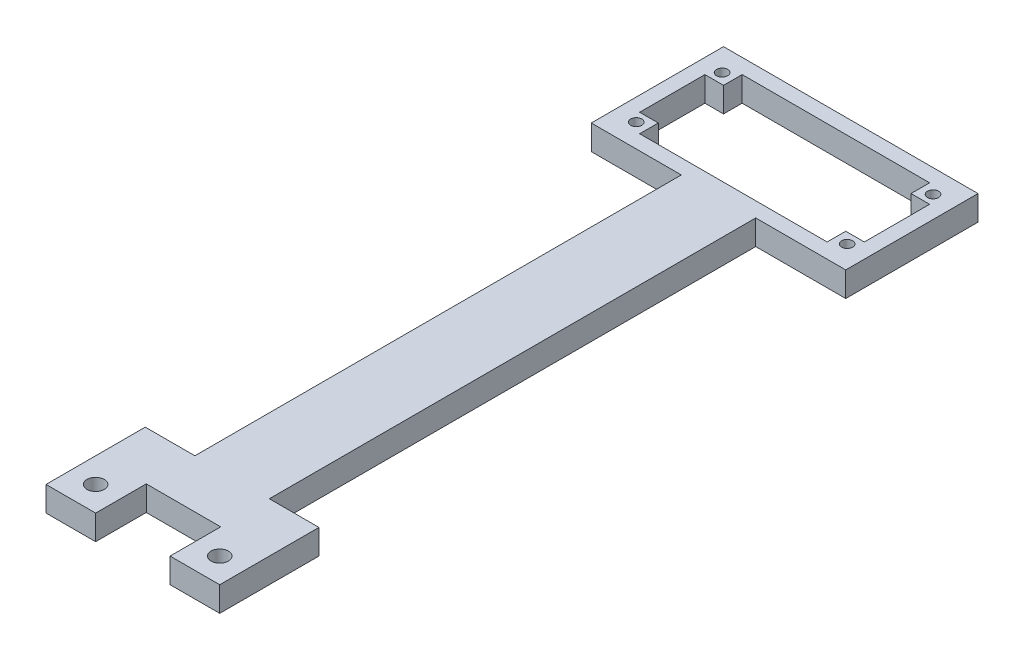
SolidWorks part; units mm, degrees
ref_plane "Front Plane" through (0, 0, 0) normal (0, 0, 1) x (1, 0, 0)
ref_plane "Top Plane" through (0, 0, 0) normal (0, 1, 0) x (1, 0, 0)
ref_plane "Right Plane" through (0, 0, 0) normal (1, 0, 0) x (0, 0, -1)
sketch "Sonic Sensor Reference Sketch" plane through (0, 0, 0) normal (0, 1, 0) x (1, 0, 0)
  line L1 (0, 0) -> (45.27, 0) construction
  line L2 (0, 0) -> (0, 20.65) construction
  line L3 (0, 20.65) -> (45.27, 20.65) construction
  line L4 (45.27, 0) -> (45.27, 20.65) construction
  dimension "D1" = 45.27
  dimension "D2" = 20.65
sketch "Sketch2" plane through (0, 0, 0) normal (0, 1, 0) x (1, 0, 0)
  line L8 (48.27, -3) -> (48.27, 23.65)
  line L9 (-3, -3) -> (48.27, -3)
  line L10 (-3, 23.65) -> (-3, -3)
  line L11 (48.27, 23.65) -> (-3, 23.65)
  line L12 (48.27, -3) -> (48.27, 23.65)
  line L13 (-3, -3) -> (48.27, -3)
  line L14 (-3, 23.65) -> (-3, -3)
  line L15 (48.27, 23.65) -> (-3, 23.65)
  dimension "D1" = 3
extrude "Boss-Extrude2" add sketch "Sketch2" along normal blind 5
sketch "Sketch3" plane through (0, 5, 0) normal (0, 1, 0) x (1, 0, 0)
  line L0 (0, 0) -> (45.27, 0) construction
  line L1 (45.27, 0) -> (45.27, 20.65) construction
  line L2 (0, 20.65) -> (45.27, 20.65) construction
  line L3 (0, 0) -> (0, 20.65) construction
  line L4 (0, 0) -> (45.27, 0)
  line L5 (45.27, 0) -> (45.27, 20.65)
  line L6 (0, 20.65) -> (45.27, 20.65)
  line L7 (0, 0) -> (0, 20.65)
extrude "Cut-Extrude1" cut sketch "Sketch3" against normal through all
sketch "Sketch4" plane through (0, 5, 0) normal (0, 1, 0) x (1, 0, 0)
  line L0 (1.385, 18.975) -> (43.885, 18.975) construction
  line L1 (22.635, 23.65) -> (22.635, -3) construction
  line L2 (48.27, 23.65) -> (-3, 23.65) construction
  line L3 (-3, -3) -> (48.27, -3) construction
  line L4 (-3, 10.325) -> (48.27, 10.325) construction
  line L5 (-3, 23.65) -> (-3, -3) construction
  line L6 (48.27, -3) -> (48.27, 23.65) construction
  line L7 (1.385, 18.975) -> (1.385, 1.675) construction
  line L8 (1.385, 1.675) -> (43.885, 1.675) construction
  line L9 (43.885, 1.675) -> (43.885, 18.975) construction
  line L11 (0, 20.65) -> (3.75, 20.65)
  line L12 (0, 20.65) -> (0, 16.9)
  line L13 (0, 16.9) -> (3.75, 16.9)
  line L14 (3.75, 20.65) -> (3.75, 16.9)
  line L15 (0, 0) -> (3.75, 0)
  line L16 (0, 0) -> (0, 3.75)
  line L17 (0, 3.75) -> (3.75, 3.75)
  line L18 (3.75, 0) -> (3.75, 3.75)
  line L19 (45.27, 0) -> (41.52, 0)
  line L20 (45.27, 0) -> (45.27, 3.75)
  line L21 (45.27, 3.75) -> (41.52, 3.75)
  line L22 (41.52, 0) -> (41.52, 3.75)
  line L23 (45.27, 20.65) -> (41.52, 20.65)
  line L24 (45.27, 20.65) -> (45.27, 16.9)
  line L25 (45.27, 16.9) -> (41.52, 16.9)
  line L26 (41.52, 20.65) -> (41.52, 16.9)
  circle A0 centre (1.385, 18.975) radius 1.12 construction
  circle A1 centre (43.885, 18.975) radius 1.12 construction
  circle A2 centre (1.385, 1.675) radius 1.12 construction
  circle A3 centre (43.885, 1.675) radius 1.12 construction
  point P17 (22.635, 18.975)
  point P18 (1.385, 10.325)
  point P42 (3.0106, 17.4014)
  dimension "D3" = 2.24
  dimension "D1" = 42.5
  dimension "D2" = 17.3
  dimension "D4" = 3.75
  dimension "D5" = 3.75
extrude "Boss-Extrude3" add sketch "Sketch4" against normal up to surface (5 mm away) up to face at (22.635, 0, -10.325)
sketch "Sketch5" plane through (0, 5, 0) normal (0, 1, 0) x (1, 0, 0)
  circle A0 centre (1.385, 18.975) radius 1.12
  circle A1 centre (43.885, 18.975) radius 1.12
  circle A2 centre (43.885, 1.675) radius 1.12
  circle A3 centre (1.385, 1.675) radius 1.12
  circle A4 centre (1.385, 18.975) radius 1.12 construction
  circle A5 centre (43.885, 18.975) radius 1.12 construction
  circle A6 centre (1.385, 1.675) radius 1.12 construction
  circle A7 centre (43.885, 1.675) radius 1.12 construction
extrude "Cut-Extrude2" cut sketch "Sketch5" against normal through all
sketch "Sketch6" plane through (0, 5, 0) normal (0, 1, 0) x (1, 0, 0)
  line L0 (-3, -3) -> (48.27, -3) construction
  line L1 (30.135, -3) -> (15.135, -3)
  line L2 (30.135, -3) -> (30.135, -111)
  line L3 (30.135, -111) -> (15.135, -111)
  line L4 (15.135, -3) -> (15.135, -111)
  point P6 (22.635, -3)
  point P7 (22.635, -3)
  point P8 (12.4878, -37.8436)
  dimension "D1" = 15
  dimension "D2" = 108
extrude "Boss-Extrude4" add sketch "Sketch6" against normal up to surface (5 mm away) up to face at (1.385, 0, -0.555)
sketch "Sketch7" plane through (0, 5, 0) normal (0, 1, 0) x (1, 0, 0)
  line L0 (30.135, -111) -> (30.135, -3) construction
  line L1 (30.135, -101) -> (40.135, -101)
  line L2 (30.135, -101) -> (30.135, -121)
  line L3 (30.135, -121) -> (40.135, -121)
  line L4 (40.135, -101) -> (40.135, -121)
  line L5 (15.135, -3) -> (15.135, -111) construction
  line L6 (15.135, -101) -> (5.135, -101)
  line L7 (15.135, -101) -> (15.135, -121)
  line L8 (15.135, -121) -> (5.135, -121)
  line L9 (5.135, -101) -> (5.135, -121)
  line L10 (15.135, -111) -> (30.135, -111) construction
  dimension "D1" = 10
  dimension "D2" = 10
  dimension "D3" = 10
  dimension "D4" = 10
  dimension "D5" = 10
  dimension "D6" = 10
extrude "Boss-Extrude5" add sketch "Sketch7" against normal up to surface (5 mm away) up to face at (1.385, 0, -0.555)
sketch "Sketch8" plane through (0, 5, 0) normal (0, 1, 0) x (1, 0, 0)
  line L0 (15.135, -111) -> (5.135, -121) construction
  line L1 (30.135, -111) -> (40.135, -121) construction
  circle A0 centre (10.135, -116) radius 1.75
  circle A1 centre (35.135, -116) radius 1.75
  dimension "D1" = 3.5
extrude "Cut-Extrude3" cut sketch "Sketch8" against normal through all
sketch "Sketch9" plane through (0, 5, 0) normal (0, 1, 0) x (1, 0, 0)
  line L1 (15.135, -111) -> (30.135, -111)
  line L2 (15.135, -111) -> (15.135, -110.8)
  line L3 (15.135, -110.8) -> (30.135, -110.8)
  line L4 (30.135, -111) -> (30.135, -110.8)
  point P5 (30.135, -53)
  dimension "D1" = 0.2
extrude "Cut-Extrude4" cut sketch "Sketch9" against normal through all
